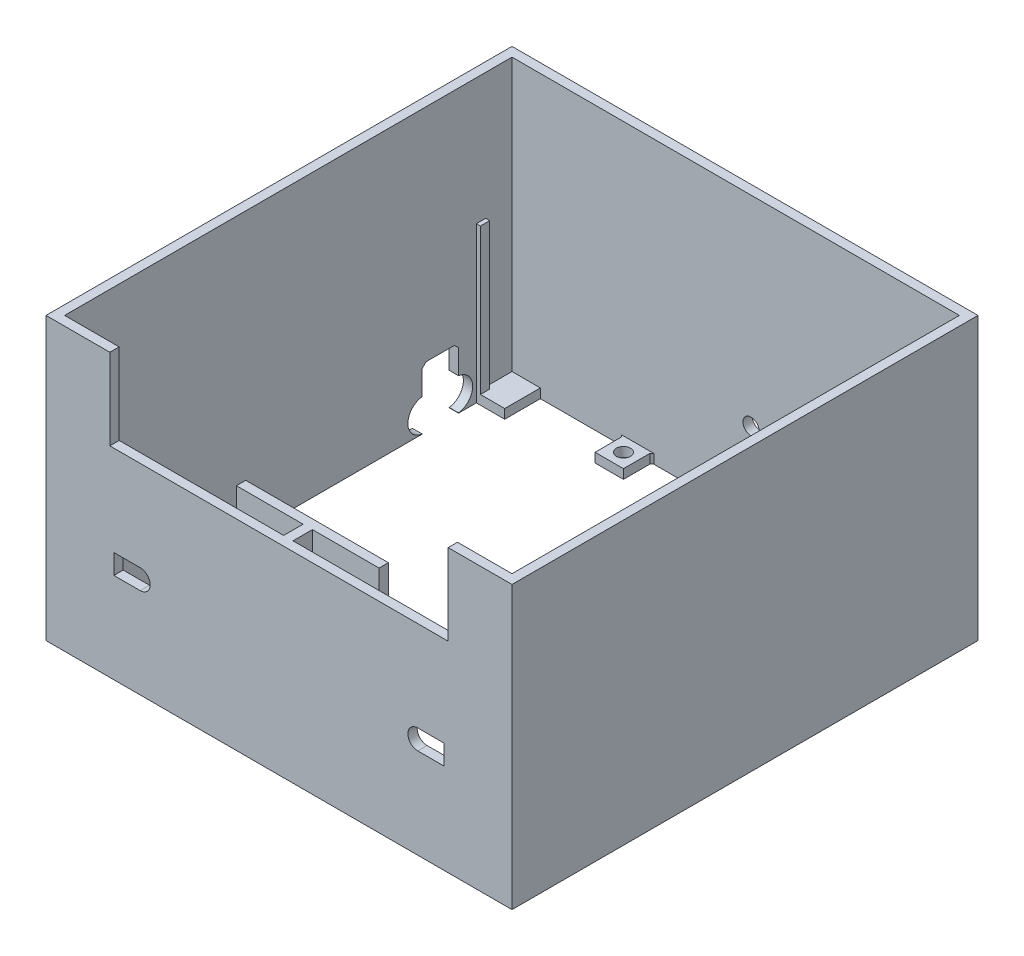
SolidWorks part; units mm, degrees
ref_plane "Front Plane" through (0, 0, 0) normal (0, 0, 1) x (1, 0, 0)
ref_plane "Top Plane" through (0, 0, 0) normal (0, 1, 0) x (1, 0, 0)
ref_plane "Right Plane" through (0, 0, 0) normal (1, 0, 0) x (0, 0, -1)
sketch "Sketch1" plane through (0, 0, 0) normal (0, 0, 1) x (1, 0, 0)
  line L1 (-17.6, 24.75) -> (17.6, 24.75)
  line L2 (-17.6, 24.75) -> (-17.6, -24.75)
  line L3 (-17.6, -24.75) -> (17.6, -24.75)
  line L4 (17.6, 24.75) -> (17.6, -24.75)
  line L5 (-17.6, 24.75) -> (17.6, -24.75) construction
  line L6 (-17.6, -24.75) -> (17.6, 24.75) construction
  point P0 (0, 0)
  dimension "D1" = 35.2
  dimension "D2" = 49.5
extrude "Boss-Extrude1" add sketch "Sketch1" along normal blind 2.3
sketch "Sketch2" plane through (0, 0, 2.3) normal (0, 0, 1) x (1, 0, 0)
  line L1 (-1.15, 24.75) -> (1.15, 24.75)
  line L2 (-1.15, 24.75) -> (-1.15, -24.75)
  line L3 (-1.15, -24.75) -> (1.15, -24.75)
  line L4 (1.15, 24.75) -> (1.15, -24.75)
  line L5 (-1.15, 24.75) -> (1.15, -24.75) construction
  line L6 (-1.15, -24.75) -> (1.15, 24.75) construction
  line L7 (-17.6, -24.75) -> (17.6, -24.75) construction
  point P0 (0, 0)
  dimension "D1" = 2.3
extrude "Boss-Extrude2" add sketch "Sketch2" along normal blind 4.8
sketch "Sketch3" plane through (0, 0, 7.1) normal (0, 0, 1) x (1, 0, 0)
  line L1 (-41.75, 24.75) -> (41.75, 24.75)
  line L2 (-41.75, 24.75) -> (-41.75, -24.75)
  line L3 (-41.75, -24.75) -> (41.75, -24.75)
  line L4 (41.75, 24.75) -> (41.75, -24.75)
  line L5 (-41.75, 24.75) -> (41.75, -24.75) construction
  line L6 (-41.75, -24.75) -> (41.75, 24.75) construction
  point P0 (0, 0)
  dimension "D1" = 83.5
  dimension "D2" = 49.5
extrude "Boss-Extrude3" add sketch "Sketch3" along normal blind 2.3
sketch "Sketch4" plane through (0, 0, 9.4) normal (0, 0, 1) x (1, 0, 0)
  line L0 (-41.75, 0) -> (41.75, 0) construction
  line L1 (-41.75, 24.75) -> (-41.75, -24.75) construction
  line L2 (41.75, -24.75) -> (41.75, 24.75) construction
  line L3 (0, 24.75) -> (0, -24.75) construction
  line L4 (41.75, 24.75) -> (-41.75, 24.75) construction
  line L5 (-41.75, -24.75) -> (41.75, -24.75) construction
  line L6 (40.75, -2.45) -> (34.25, -2.45)
  line L7 (-40.75, 2.45) -> (-34.25, 2.45)
  line L8 (-40.75, 2.45) -> (-40.75, -2.45)
  line L9 (-40.75, -2.45) -> (-34.25, -2.45)
  line L10 (-34.25, 2.45) -> (-34.25, -2.45)
  line L11 (-40.75, 2.45) -> (-34.25, -2.45) construction
  line L12 (-40.75, -2.45) -> (-34.25, 2.45) construction
  line L13 (34.25, 2.45) -> (34.25, -2.45)
  line L14 (40.75, 2.45) -> (34.25, 2.45)
  line L15 (40.75, 2.45) -> (40.75, -2.45)
  circle A0 centre (-34.25, 0) radius 2.45
  circle A1 centre (34.25, 0) radius 2.45
  point P12 (-37.5, 0)
  dimension "D1" = 6.5
  dimension "D2" = 4.9
  dimension "D3" = 1
extrude "Cut-Extrude1" cut sketch "Sketch4" against normal through all contours A0 L7 L8 L9 | L10 A0 | L10 A0 | A1 L13 | A1 L13 | L14 A1 L6 L15
sketch "Sketch10" plane through (0, -24.75, 0) normal (0, -1, 0) x (1, 0, 0)
  line L1 (-41.75, 9.4) -> (-57.5, 9.4)
  line L2 (-41.75, 9.4) -> (-41.75, 7.1)
  line L3 (-41.75, 7.1) -> (-57.5, 7.1)
  line L4 (-57.5, 9.4) -> (-57.5, 7.1)
  line L5 (41.75, 9.4) -> (57.5, 9.4)
  line L6 (41.75, 9.4) -> (41.75, 7.1)
  line L7 (41.75, 7.1) -> (57.5, 7.1)
  line L8 (57.5, 9.4) -> (57.5, 7.1)
  line L9 (-57.5, 7.1) -> (-55.2, 7.1)
  line L10 (-57.5, 7.1) -> (-57.5, -105.6)
  line L11 (-57.5, -105.6) -> (-55.2, -105.6)
  line L12 (-55.2, 7.1) -> (-55.2, -105.6)
  line L13 (57.5, 7.1) -> (55.2, 7.1)
  line L14 (57.5, 7.1) -> (57.5, -105.6)
  line L15 (57.5, -105.6) -> (55.2, -105.6)
  line L16 (55.2, 7.1) -> (55.2, -105.6)
  line L17 (-55.2, -105.6) -> (55.2, -105.6)
  line L18 (-55.2, -105.6) -> (-55.2, -103.3)
  line L19 (-55.2, -103.3) -> (55.2, -103.3)
  line L20 (55.2, -105.6) -> (55.2, -103.3)
  dimension "D1" = 15.75
  dimension "D2" = 15.75
  dimension "D3" = 115
  dimension "D4" = 115
  dimension "D5" = 2.3
  dimension "D6" = 2.3
  dimension "D7" = 2.3
extrude "Boss-Extrude10" add sketch "Sketch10" against normal offset from surface (69.5 mm away) 20 contours L19 L12 L17 L16 | L7 L16 L15 L14 | L12 L3 L10 L11 up to face at (0, 24.75, 4.7) offset beyond the face yes
sketch "Sketch7" plane through (0, -24.75, 0) normal (0, -1, 0) x (1, 0, 0)
  line L0 (-55.2, 7.1) -> (-1.15, 7.1) construction
  line L1 (-27.7, 7.1) -> (-20.7, 7.1)
  line L2 (-27.7, 7.1) -> (-27.7, 0.1)
  line L3 (-27.7, 0.1) -> (-20.7, 0.1)
  line L4 (-20.7, 7.1) -> (-20.7, 0.1)
  line L5 (0, 9.4) -> (0, 0) construction
  line L6 (-57.5, 9.4) -> (57.5, 9.4) construction
  line L7 (-27.7, 7.1) -> (-20.7, 0.1) construction
  line L8 (27.7, 0.1) -> (20.7, 0.1)
  line L9 (20.7, 7.1) -> (20.7, 0.1)
  line L10 (27.7, 7.1) -> (20.7, 7.1)
  line L11 (27.7, 7.1) -> (27.7, 0.1)
  line L12 (-55.2, -48.1) -> (55.2, -48.1) construction
  line L13 (-55.2, 7.1) -> (-55.2, -103.3) construction
  line L14 (55.2, 7.1) -> (55.2, -103.3) construction
  line L15 (27.7, -103.3) -> (27.7, -96.3)
  line L16 (27.7, -103.3) -> (20.7, -103.3)
  line L17 (20.7, -103.3) -> (20.7, -96.3)
  line L18 (27.7, -96.3) -> (20.7, -96.3)
  line L19 (-27.7, -96.3) -> (-20.7, -96.3)
  line L20 (-20.7, -103.3) -> (-20.7, -96.3)
  line L21 (-27.7, -103.3) -> (-20.7, -103.3)
  line L22 (-27.7, -103.3) -> (-27.7, -96.3)
  circle A0 centre (-24.2, 3.6) radius 1.75
  circle A1 centre (24.2, 3.6) radius 1.75
  circle A2 centre (24.2, -99.8) radius 1.75
  circle A3 centre (-24.2, -99.8) radius 1.75
  dimension "D4" = 3.5
  dimension "D1" = 3.1
  dimension "D2" = 7
  dimension "D3" = 7
extrude "Boss-Extrude7" add sketch "Sketch7" against normal blind 2.3
chamfer "Chamfer1" distance 0.5 angle 45 8 edges at (-27.7, -23.6, 7.1) (-20.7, -23.6, 7.1) (20.7, -23.6, 7.1) (27.7, -23.6, 7.1) (27.7, -23.6, -103.3) (20.7, -23.6, -103.3) (-20.7, -23.6, -103.3) (-27.7, -23.6, -103.3)
sketch "Sketch12" plane through (0, 0, -103.3) normal (0, 0, 1) x (1, 0, 0)
  line L5 (-55.2, 44.75) -> (-55.2, -24.75) construction
  line L10 (0, 44.75) -> (0, -24.75) construction
  line L11 (55.2, -24.75) -> (48.2, -24.75)
  line L12 (48.2, -22.45) -> (48.2, -24.75)
  line L14 (-55.2, -22.45) -> (-48.2, -22.45)
  line L15 (-55.2, -22.45) -> (-55.2, -24.75)
  line L16 (-55.2, -24.75) -> (-48.2, -24.75)
  line L17 (-48.2, -22.45) -> (-48.2, -24.75)
  line L20 (55.2, 44.75) -> (-55.2, 44.75) construction
  line L21 (-20.2, -24.75) -> (20.2, -24.75) construction
  line L22 (55.2, -22.45) -> (48.2, -22.45)
  line L23 (55.2, -22.45) -> (55.2, -24.75)
  point P17 (0, 0)
  dimension "D6" = 7
  dimension "D7" = 2.3
extrude "Boss-Extrude11" add sketch "Sketch12" along normal blind 8.8
sketch "Sketch13" plane through (0, -22.45, 0) normal (0, 1, 0) x (1, 0, 0)
  line L0 (-55.2, 94.5) -> (-55.2, 103.3) construction
  line L1 (55.2, 94.5) -> (52.9, 94.5)
  line L2 (55.2, 94.5) -> (55.2, 96.8)
  line L3 (55.2, 96.8) -> (52.9, 96.8)
  line L4 (52.9, 94.5) -> (52.9, 96.8)
  line L5 (-55.2, 96.8) -> (-54.2, 96.8)
  line L6 (-55.2, 96.8) -> (-55.2, 94.5)
  line L7 (-55.2, 94.5) -> (-54.2, 94.5)
  line L8 (-54.2, 96.8) -> (-54.2, 94.5)
  line L9 (-48.2, 94.5) -> (-55.2, 94.5) construction
  point P14 (0, 0)
  dimension "D1" = 2.3
  dimension "D2" = 2.3
  dimension "D3" = 1
  dimension "D4" = 2.3
extrude "Boss-Extrude12" add sketch "Sketch13" along normal blind 36
sketch "Sketch14" plane through (0, 0, -103.3) normal (0, 0, 1) x (1, 0, 0)
  line L0 (55.2, -4.7) -> (-55.2, -4.7) construction
  line L3 (55.2, -22.45) -> (48.2, -22.45) construction
  line L4 (0.8, -1.7) -> (6.8, -1.7) construction
  line L5 (0.8, -1.7) -> (0.8, -7.7) construction
  line L6 (0.8, -7.7) -> (6.8, -7.7) construction
  line L7 (6.8, -1.7) -> (6.8, -7.7) construction
  line L8 (0.8, -1.7) -> (6.8, -7.7) construction
  line L9 (0.8, -7.7) -> (6.8, -1.7) construction
  line L10 (55.2, 44.75) -> (55.2, -22.45) construction
  line L11 (-55.2, 44.75) -> (-55.2, -22.45) construction
  circle A0 centre (46.7, -4.7) radius 1
  circle A1 centre (38.2, -4.7) radius 1
  circle A2 centre (29.7, -4.7) radius 1
  circle A3 centre (21.2, -4.7) radius 1
  circle A4 centre (3.8, -4.7) radius 2
  point P2 (53.5362, 13.5183)
  point P4 (-53.8351, 11.15)
  point P14 (3.8, -4.7)
  point P21 (0, 0)
  point P24 (-52.0662, -4.7)
  dimension "D1" = 8.5
  dimension "D5" = 2
  dimension "D6" = 2
  dimension "D7" = 2
  dimension "D8" = 2
  dimension "D12" = 4
  dimension "D2" = 17
  dimension "D3" = 25.5
  dimension "D4" = 34
  dimension "D9" = 54.4
  dimension "D10" = 6
  dimension "D11" = 6
  dimension "D13" = 17.75
extrude "Cut-Extrude3" cut sketch "Sketch14" against normal through all
sketch "Sketch18" plane through (-57.5, 0, 0) normal (-1, 0, 0) x (0, 0, 1)
  line L0 (-85.6, -9.75) -> (-85.6, -24.75) construction
  line L1 (-90.1, -9.75) -> (-81.1, -9.75)
  line L2 (-90.1, -9.75) -> (-90.1, -24.75)
  line L3 (-90.1, -24.75) -> (-81.1, -24.75)
  line L4 (-81.1, -9.75) -> (-81.1, -24.75)
  line L5 (9.4, -24.75) -> (-105.6, -24.75) construction
  circle A0 centre (-89.6, -20.71) radius 4
  circle A1 centre (-81.6, -20.71) radius 4
  point P8 (-85.6, -20.71)
  point P13 (0, 0)
  point P14 (0, 0)
  dimension "D1" = 20
  dimension "D3" = 8
  dimension "D4" = 8
  dimension "D2" = 9
  dimension "D5" = 8
  dimension "D6" = 15
extrude "Cut-Extrude4" cut sketch "Sketch18" against normal up to next contours L2 A0 | L4 A1
chamfer "Chamfer2" distance 1 angle 45 2 edges at (-56.35, -9.75, -81.1) (-56.35, -9.75, -90.1)
